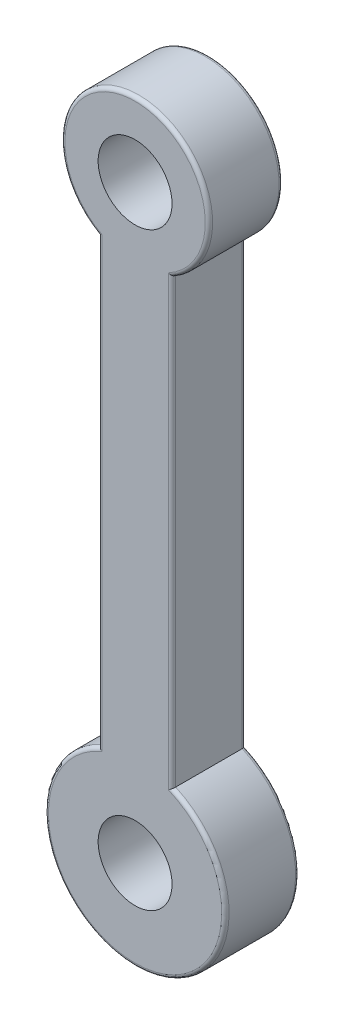
SolidWorks part; units mm, degrees
material "Plain Carbon Steel"
ref_plane "Plan de face" through (0, 0, 0) normal (0, 0, 1) x (1, 0, 0)
ref_plane "Plan de dessus" through (0, 0, 0) normal (0, 1, 0) x (1, 0, 0)
ref_plane "Plan de droite" through (0, 0, 0) normal (1, 0, 0) x (0, 0, -1)
sketch "Esquisse1" plane through (0, 0, 0) normal (0, 0, 1) x (1, 0, 0)
  line L1 (-10, -17.3205) -> (-10, -137.3205)
  line L2 (10, -17.3205) -> (10, -137.3205)
  circle A0 centre (0, 0) radius 10
  arc A1 (10, -17.3205) -> (-10, -17.3205) centre (0, 0) ccw
  circle A2 centre (0, -159.641) radius 10
  arc A3 (-10, -137.3205) -> (10, -137.3205) centre (0, -159.641) ccw
  point P7 (-10, 0)
  point P8 (-10, -70)
  point P9 (10, 0)
  point P10 (10, -70)
  dimension "D1" = 120
  dimension "D2" = 120
extrude "Boss.-Extru.1" add sketch "Esquisse1" along normal blind 20
fillet "Congé2" radius 1 8 edges at (0, -184.0992, 20) (-10, -77.3205, 20) (0, 20, 20) (10, -77.3205, 20) (10, -77.3205, 0) (0, -184.0992, 0) (-10, -77.3205, 0) (0, 20, 0)
sketch "Sketch2" plane through (0, 0, 20) normal (0, 0, 1) x (1, 0, 0)
  point P0 (0, -159.641)
  point P1 (0, 0)
sketch "Sketch3" plane through (0, 0, 0) normal (0, 0, -1) x (-1, 0, 0)
  point P0 (0, -159.641)
sketch "Sketch4" plane through (0, 0, 20) normal (0, 0, 1) x (1, 0, 0)
  line L0 (0, 0) -> (0, -159.641) construction
  line L1 (0, 0) -> (0, -80) construction
  point P0 (0, -80)
  dimension "D1" = 80
  dimension "D2" = 0
sketch "Sketch5" plane through (0, 0, 20) normal (0, 0, 1) x (1, 0, 0)
  line L0 (0, 0) -> (0, -159.641) construction
  point P0 (0, -120)
  point P1 (0, -40)
  dimension "D1" = 40
  dimension "D2" = 40
